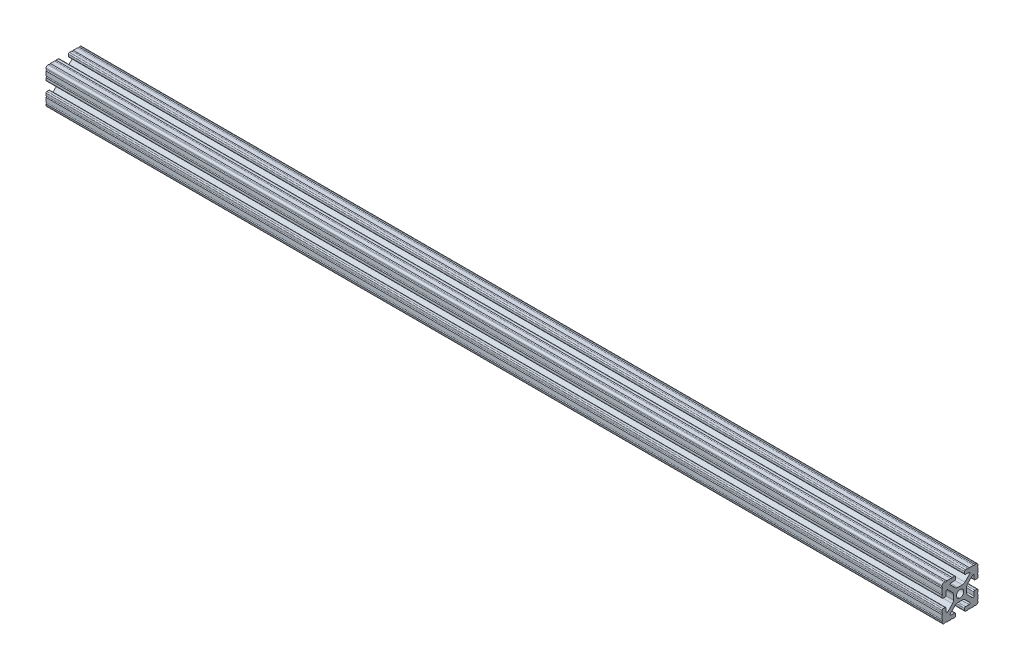
SolidWorks part; units mm, degrees
ref_plane "Front Plane" through (0, 0, 0) normal (0, 0, 1) x (1, 0, 0)
ref_plane "Top Plane" through (0, 0, 0) normal (0, 1, 0) x (1, 0, 0)
ref_plane "Right Plane" through (0, 0, 0) normal (1, 0, 0) x (0, 0, -1)
sketch "Sketch3"
sketch "Sketch2" plane through (0, 0, 0) normal (1, 0, 0) x (0, 0, -1)
  line L0 (16.1207, 7.3347) -> (19.544, 3.9114)
  line L1 (17.3256, 11.0651) -> (17.3256, 14.3349)
  line L2 (18.0653, 16.1207) -> (21.4886, 19.544)
  line L3 (22.598, 16.6362) -> (22.598, 19.0845)
  line L4 (24.7023, 15.9385) -> (23.2956, 15.9385)
  line L6 (2.1006, 25.4) -> (1.3474, 25.4)
  line L7 (16.6362, 2.802) -> (19.0845, 2.802)
  line L8 (0.6977, 15.9385) -> (2.1044, 15.9385)
  line L9 (2.802, 16.6362) -> (2.802, 19.0845)
  line L10 (0, 16.6362) -> (0, 18.2699)
  line L11 (8.0744, 11.0651) -> (8.0744, 14.3349)
  line L12 (7.3347, 16.1207) -> (3.9114, 19.544)
  line L13 (0, 19.2426) -> (0, 22.318)
  line L14 (0, 23.2994) -> (0, 24.0526)
  line L15 (6.1574, 25.4) -> (3.082, 25.4)
  line L16 (8.7638, 25.4) -> (7.1301, 25.4)
  line L17 (9.4615, 24.7023) -> (9.4615, 23.2956)
  line L18 (8.7638, 22.598) -> (6.3155, 22.598)
  line L19 (9.2793, 18.0653) -> (5.856, 21.4886)
  line L20 (14.3349, 17.3256) -> (11.0651, 17.3256)
  line L22 (25.4, 16.6362) -> (25.4, 18.2699)
  line L23 (25.4, 19.2426) -> (25.4, 22.318)
  line L24 (25.4, 23.2994) -> (25.4, 24.0526)
  line L25 (23.2994, 25.4) -> (24.0526, 25.4)
  line L26 (19.2426, 25.4) -> (22.318, 25.4)
  line L27 (16.6362, 25.4) -> (18.2699, 25.4)
  line L28 (15.9385, 24.7023) -> (15.9385, 23.2956)
  line L29 (16.6362, 22.598) -> (19.0845, 22.598)
  line L30 (16.1207, 18.0653) -> (19.544, 21.4886)
  line L31 (15.9385, 0.6977) -> (15.9385, 2.1044)
  line L32 (16.6362, 0) -> (18.2699, 0)
  line L33 (19.2426, 0) -> (22.318, 0)
  line L34 (23.2994, 0) -> (24.0526, 0)
  line L35 (25.4, 2.1006) -> (25.4, 1.3474)
  line L36 (25.4, 6.1574) -> (25.4, 3.082)
  line L37 (25.4, 8.7638) -> (25.4, 7.1301)
  line L38 (14.3349, 8.0744) -> (11.0651, 8.0744)
  line L39 (9.2793, 7.3347) -> (5.856, 3.9114)
  line L40 (8.7638, 2.802) -> (6.3155, 2.802)
  line L41 (9.4615, 0.6977) -> (9.4615, 2.1044)
  line L42 (8.7638, 0) -> (7.1301, 0)
  line L43 (6.1574, 0) -> (3.082, 0)
  line L44 (0, 2.1006) -> (0, 1.3474)
  line L45 (0, 6.1574) -> (0, 3.082)
  line L46 (7.3347, 9.2793) -> (3.9114, 5.856)
  line L47 (0, 8.7638) -> (0, 7.1301)
  line L48 (2.802, 8.7638) -> (2.802, 6.3155)
  line L49 (0.6977, 9.4615) -> (2.1044, 9.4615)
  line L50 (2.1006, 0) -> (1.3474, 0)
  line L51 (24.7023, 9.4615) -> (23.2956, 9.4615)
  line L52 (22.598, 8.7638) -> (22.598, 6.3155)
  line L53 (18.0653, 9.2793) -> (21.4886, 5.856)
  circle A0 centre (12.7, 12.7) radius 2.6035
  arc A1 (7.3347, 16.1207) -> (8.0744, 14.3349) centre (5.5489, 14.3349) cw
  arc A2 (2.802, 19.0845) -> (3.9114, 19.544) centre (3.4519, 19.0845) cw
  arc A3 (2.802, 16.6362) -> (2.1044, 15.9385) centre (2.1044, 16.6362) cw
  arc A4 (0, 16.6362) -> (0.6977, 15.9385) centre (0.6977, 16.6362) ccw
  arc A5 (-0.0204, 18.2642) -> (-0.0101, 19.2455) centre (-0.1467, 18.7562) ccw
  arc A6 (0, 22.318) -> (0, 23.2994) centre (-0.1315, 22.8087) ccw
  arc A7 (0, 24.0526) -> (1.3474, 25.4) centre (1.3474, 24.0526) cw
  arc A8 (3.082, 25.4) -> (2.1006, 25.4) centre (2.5913, 25.5315) cw
  arc A9 (7.1358, 25.4204) -> (6.1545, 25.4101) centre (6.6438, 25.5467) cw
  arc A10 (8.7638, 25.4) -> (9.4615, 24.7023) centre (8.7638, 24.7023) cw
  arc A11 (8.7638, 22.598) -> (9.4615, 23.2956) centre (8.7638, 23.2956) ccw
  arc A12 (6.3155, 22.598) -> (5.856, 21.4886) centre (6.3155, 21.9481) ccw
  arc A13 (9.2793, 18.0653) -> (11.0651, 17.3256) centre (11.0651, 19.8511) ccw
  arc A14 (18.0653, 16.1207) -> (17.3256, 14.3349) centre (19.8511, 14.3349) ccw
  arc A15 (22.598, 19.0845) -> (21.4886, 19.544) centre (21.9481, 19.0845) ccw
  arc A16 (22.598, 16.6362) -> (23.2956, 15.9385) centre (23.2956, 16.6362) ccw
  arc A17 (25.4, 16.6362) -> (24.7023, 15.9385) centre (24.7023, 16.6362) cw
  arc A18 (25.4204, 18.2642) -> (25.4101, 19.2455) centre (25.5467, 18.7562) cw
  arc A19 (25.4, 22.318) -> (25.4, 23.2994) centre (25.5315, 22.8087) cw
  arc A20 (25.4, 24.0526) -> (24.0526, 25.4) centre (24.0526, 24.0526) ccw
  arc A21 (22.318, 25.4) -> (23.2994, 25.4) centre (22.8087, 25.5315) ccw
  arc A22 (18.2642, 25.4204) -> (19.2455, 25.4101) centre (18.7562, 25.5467) ccw
  arc A23 (16.6362, 25.4) -> (15.9385, 24.7023) centre (16.6362, 24.7023) ccw
  arc A24 (16.6362, 22.598) -> (15.9385, 23.2956) centre (16.6362, 23.2956) cw
  arc A25 (19.0845, 22.598) -> (19.544, 21.4886) centre (19.0845, 21.9481) cw
  arc A26 (16.1207, 18.0653) -> (14.3349, 17.3256) centre (14.3349, 19.8511) cw
  arc A27 (16.1207, 7.3347) -> (14.3349, 8.0744) centre (14.3349, 5.5489) ccw
  arc A28 (19.0845, 2.802) -> (19.544, 3.9114) centre (19.0845, 3.4519) ccw
  arc A29 (16.6362, 2.802) -> (15.9385, 2.1044) centre (16.6362, 2.1044) ccw
  arc A30 (16.6362, 0) -> (15.9385, 0.6977) centre (16.6362, 0.6977) cw
  arc A31 (18.2642, -0.0204) -> (19.2455, -0.0101) centre (18.7562, -0.1467) cw
  arc A32 (22.318, 0) -> (23.2994, 0) centre (22.8087, -0.1315) cw
  arc A33 (25.4, 1.3474) -> (24.0526, 0) centre (24.0526, 1.3474) cw
  arc A34 (25.4, 3.082) -> (25.4, 2.1006) centre (25.5315, 2.5913) ccw
  arc A35 (25.4204, 7.1358) -> (25.4101, 6.1545) centre (25.5467, 6.6438) ccw
  arc A36 (25.4, 8.7638) -> (24.7023, 9.4615) centre (24.7023, 8.7638) ccw
  arc A37 (22.598, 8.7638) -> (23.2956, 9.4615) centre (23.2956, 8.7638) cw
  arc A38 (22.598, 6.3155) -> (21.4886, 5.856) centre (21.9481, 6.3155) cw
  arc A39 (18.0653, 9.2793) -> (17.3256, 11.0651) centre (19.8511, 11.0651) cw
  arc A40 (9.2793, 7.3347) -> (11.0651, 8.0744) centre (11.0651, 5.5489) cw
  arc A41 (6.3155, 2.802) -> (5.856, 3.9114) centre (6.3155, 3.4519) cw
  arc A42 (8.7638, 2.802) -> (9.4615, 2.1044) centre (8.7638, 2.1044) cw
  arc A43 (8.7638, 0) -> (9.4615, 0.6977) centre (8.7638, 0.6977) ccw
  arc A44 (7.1358, -0.0204) -> (6.1545, -0.0101) centre (6.6438, -0.1467) ccw
  arc A45 (3.082, 0) -> (2.1006, 0) centre (2.5913, -0.1315) ccw
  arc A46 (0, 1.3474) -> (1.3474, 0) centre (1.3474, 1.3474) ccw
  arc A47 (0, 3.082) -> (0, 2.1006) centre (-0.1315, 2.5913) cw
  arc A48 (-0.0204, 7.1358) -> (-0.0101, 6.1545) centre (-0.1467, 6.6438) cw
  arc A49 (0, 8.7638) -> (0.6977, 9.4615) centre (0.6977, 8.7638) cw
  arc A50 (2.802, 8.7638) -> (2.1044, 9.4615) centre (2.1044, 8.7638) ccw
  arc A51 (2.802, 6.3155) -> (3.9114, 5.856) centre (3.4519, 6.3155) ccw
  arc A52 (7.3347, 9.2793) -> (8.0744, 11.0651) centre (5.5489, 11.0651) ccw
  point P100 (12.7, 17.3256)
  point P181 (8.0744, 12.7)
  point P182 (17.3256, 12.7)
extrude "Boss-Extrude1" add sketch "Sketch2" along normal blind 635 contours A52 L46 A51 L48 A50 L49 A49 L47 A48 L45 A47 L44 A46 L50 A45 L43 A44 L42 A43 L41 A42 L40 A41 L39 A40 L38 A27 L0 A28 L7 A29 L31 A30 L32 A31 L33 A32 L34 A33 L35 A34 L36 A35 L37 A36 L51 A37 L52 A38 L53 A39
move or copy body "Body-Move/Copy1" bodies to move or copy 102 copy no translate (-150.0587, 28.7597, 59.645)
sketch "Sketch4" plane through (0, 0, 0) normal (0, 0, 1) x (1, 0, 0)
  line L0 (484.9413, 54.1597) -> (-150.0587, 54.1597) construction
  line L1 (-78.6761, 54.1597) -> (-106.0407, -11.9043)
  line L2 (378.5239, 54.1597) -> (405.8885, -11.9043)
  line L3 (405.8885, -11.9043) -> (480.3446, -42.745)
  line L4 (480.3446, -42.745) -> (535.2221, 89.7411)
  line L5 (535.2221, 89.7411) -> (378.5239, 89.7411)
  line L6 (378.5239, 89.7411) -> (378.5239, 54.1597)
  line L7 (-78.6761, 54.1597) -> (-78.6761, 92.6727)
  line L8 (-78.6761, 92.6727) -> (-197.9311, 43.2757)
  line L9 (-197.9311, 43.2757) -> (-164.965, -36.3115)
  line L10 (-164.965, -36.3115) -> (-106.0407, -11.9043)
  dimension "D1" = 67.5
  dimension "D2" = 67.5
